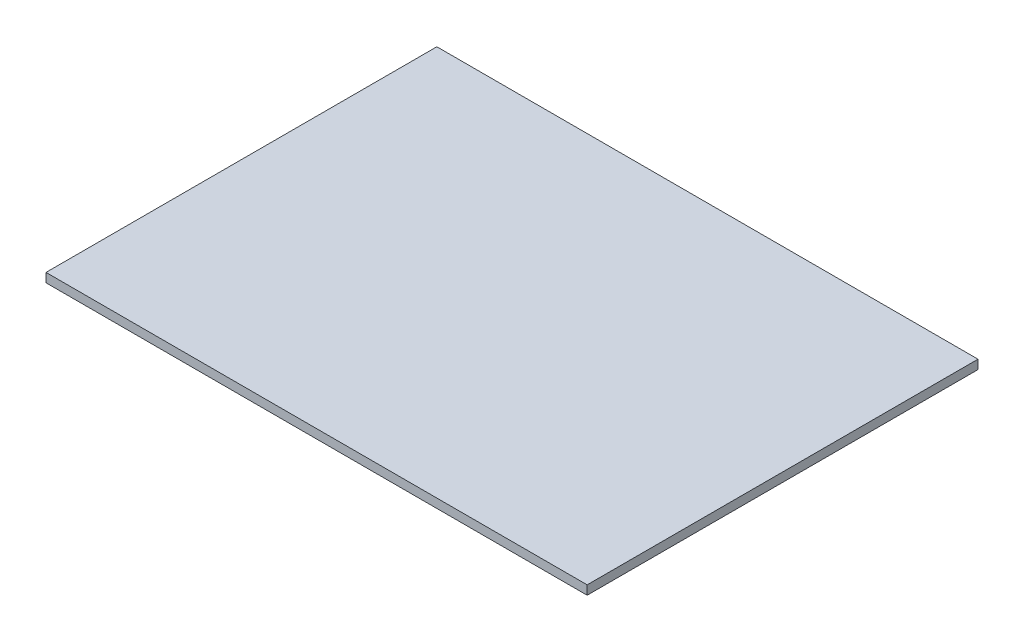
SolidWorks part; units mm, degrees
ref_plane "Front Plane" through (0, 0, 0) normal (0, 0, 1) x (1, 0, 0)
ref_plane "Top Plane" through (0, 0, 0) normal (0, 1, 0) x (1, 0, 0)
ref_plane "Right Plane" through (0, 0, 0) normal (1, 0, 0) x (0, 0, -1)
sketch "Sketch1" plane through (0, 0, 0) normal (0, 0, 1) x (1, 0, 0)
  line L0 (0, 0) -> (0, 15)
  dimension "D1" = 15
extrude "Extrude-Thin1" add sketch "Sketch1" along normal mid plane 650 thin thin type mid plane wall 900
